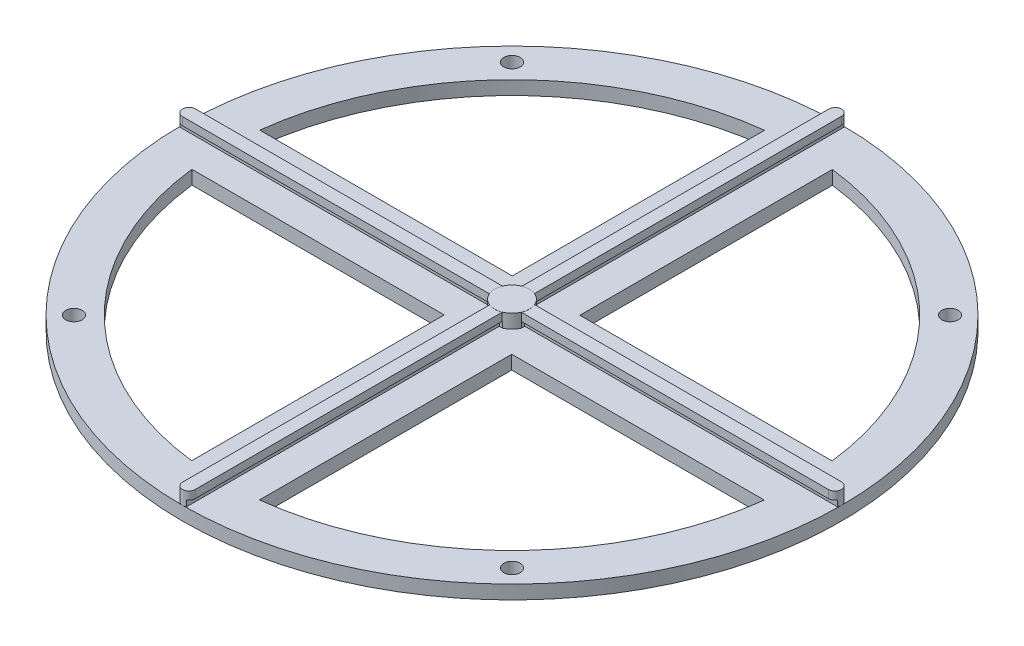
SolidWorks part; units mm, degrees
ref_plane "Front Plane" through (0, 0, 0) normal (0, 0, 1) x (1, 0, 0)
ref_plane "Top Plane" through (0, 0, 0) normal (0, 1, 0) x (1, 0, 0)
ref_plane "Right Plane" through (0, 0, 0) normal (1, 0, 0) x (0, 0, -1)
sketch "Sketch1" plane through (0, 0, 0) normal (0, 1, 0) x (1, 0, 0)
  circle A0 centre (0, 0) radius 76.2
  dimension "D1" = 152.4
extrude "Boss-Extrude1" add sketch "Sketch1" along normal blind 3.175
sketch "Sketch2" plane through (0, 3.175, 0) normal (0, 1, 0) x (1, 0, 0)
  line L0 (0, -76.2) -> (0, 76.2)
  line L1 (-76.2, 0) -> (76.2, 0)
  line L2 (-74.676, 0) -> (74.676, 0) construction
  line L3 (-74.676, 1.524) -> (74.676, 1.524)
  line L4 (-74.676, -1.524) -> (74.676, -1.524)
  line L5 (0, 74.7395) -> (0, -74.7395) construction
  line L6 (1.4605, 74.7395) -> (1.4605, -74.7395)
  line L7 (-1.4605, 74.7395) -> (-1.4605, -74.7395)
  circle A0 centre (0, 0) radius 76.2 construction
  arc A1 (-74.676, 1.524) -> (-74.676, -1.524) centre (-74.676, 0) ccw
  arc A2 (74.676, -1.524) -> (74.676, 1.524) centre (74.676, 0) ccw
  arc A3 (1.4605, 74.7395) -> (-1.4605, 74.7395) centre (0, 74.7395) ccw
  arc A4 (-1.4605, -74.7395) -> (1.4605, -74.7395) centre (0, -74.7395) ccw
  point P7 (0, 0)
  point P11 (0, 0)
  point P12 (0, 0)
  point P19 (0, 0)
  dimension "D1" = 3.048
  dimension "D2" = 2.921
extrude "Boss-Extrude2" add sketch "Sketch2" along normal blind 3.175 contours L7 A4 L6 A3 | L4 A1 L3 A2
sketch "Sketch3" plane through (0, 6.35, 0) normal (0, 1, 0) x (1, 0, 0)
  circle A0 centre (0, 0) radius 4
  dimension "D1" = 8
extrude "Boss-Extrude3" add sketch "Sketch3" along normal blind 0.0254 and the other way up to surface (6.35 mm away)
sketch "Sketch4" plane through (0, 3.175, 0) normal (0, 1, 0) x (1, 0, 0)
  line L0 (-7.8105, 7.874) -> (-39.5605, 7.874)
  line L1 (-74.676, 1.524) -> (-3.6983, 1.524) construction
  line L2 (-1.4605, 74.7395) -> (-1.4605, 3.7238) construction
  line L3 (-7.8105, 7.874) -> (-7.8105, 63.0178)
  line L4 (-39.5605, 7.874) -> (-63.0099, 7.874)
  line L5 (-7.8105, 63.0178) -> (-7.8105, 66.2159)
  line L6 (-63.0099, 7.874) -> (-66.2084, 7.874)
  line L7 (7.874, 63.0099) -> (7.874, 66.2084)
  line L8 (7.874, 39.5605) -> (7.874, 63.0099)
  line L9 (7.874, 7.8105) -> (7.874, 39.5605)
  line L10 (7.874, 7.8105) -> (63.0178, 7.8105)
  line L11 (63.0178, 7.8105) -> (66.2159, 7.8105)
  line L12 (63.0099, -7.874) -> (66.2084, -7.874)
  line L13 (39.5605, -7.874) -> (63.0099, -7.874)
  line L14 (7.8105, -7.874) -> (39.5605, -7.874)
  line L15 (7.8105, -7.874) -> (7.8105, -63.0178)
  line L16 (7.8105, -63.0178) -> (7.8105, -66.2159)
  line L17 (-7.874, -63.0099) -> (-7.874, -66.2084)
  line L18 (-7.874, -39.5605) -> (-7.874, -63.0099)
  line L19 (-7.874, -7.8105) -> (-7.874, -39.5605)
  line L20 (-7.874, -7.8105) -> (-63.0178, -7.8105)
  line L21 (-63.0178, -7.8105) -> (-66.2159, -7.8105)
  arc A2 (-7.8105, 66.2159) -> (-66.2084, 7.874) centre (0, 0) ccw
  arc A3 (66.2159, 7.8105) -> (7.874, 66.2084) centre (0, 0) ccw
  arc A4 (7.8105, -66.2159) -> (66.2084, -7.874) centre (0, 0) ccw
  arc A5 (-66.2159, -7.8105) -> (-7.874, -66.2084) centre (0, 0) ccw
  point P34 (0, 0)
  dimension "D1" = 6.35
  dimension "D3" = 4
  dimension "D2" = 6.35
extrude "Cut-Extrude1" cut sketch "Sketch4" against normal through all
sketch "Sketch6" plane through (0, 0, 1.524) normal (0, 0, 1) x (1, 0, 0)
  line L0 (3.6983, 3.175) -> (3.6983, 4.5085)
  line L1 (3.6983, 6.35) -> (3.6983, 3.175) construction
  line L2 (3.6983, 4.5085) -> (76.2, 4.5085)
  line L3 (76.2, 3.175) -> (76.2, 6.35) construction
  line L4 (76.2, 4.5085) -> (76.2, 3.175)
  line L5 (76.2, 3.175) -> (3.6983, 3.175)
extrude "Cut-Extrude3" cut sketch "Sketch6" against normal blind 0.762
pattern_circular "CirPattern1" count 4 over 360 about axis through (0, 0, 0) along (0, 1, 0) of "Cut-Extrude3"
sketch "Sketch7" plane through (0, 0, -1.524) normal (0, 0, -1) x (-1, 0, 0)
  line L0 (-3.6983, 3.175) -> (-3.6983, 4.5085)
  line L1 (-3.6983, 6.35) -> (-3.6983, 3.175) construction
  line L2 (-3.6983, 4.5085) -> (-77.7609, 4.5085)
  line L3 (-77.7609, 4.5085) -> (-77.7609, 3.175)
  line L4 (-77.7609, 3.175) -> (-3.6983, 3.175)
extrude "Cut-Extrude4" cut sketch "Sketch7" against normal blind 0.762
pattern_circular "CirPattern2" count 4 over 360 about axis through (0, 0, 0) along (0, 1, 0) of "Cut-Extrude4"
sketch "Sketch8" plane through (0, 3.175, 0) normal (0, 1, 0) x (1, 0, 0)
  line L0 (0, 0) -> (-53.8815, -53.8815) construction
  arc A0 (-76.2, 0) -> (0, -76.2) centre (0, 0) ccw construction
  circle A1 centre (-50.6486, -50.6486) radius 1.905
  circle A2 centre (-50.6486, 50.6486) radius 1.905
  circle A3 centre (50.6486, 50.6486) radius 1.905
  circle A4 centre (50.6486, -50.6486) radius 1.905
  point P18 (0, 0)
  dimension "D1" = 4.572
  dimension "D2" = 4
extrude "Cut-Extrude5" cut sketch "Sketch8" against normal through all
